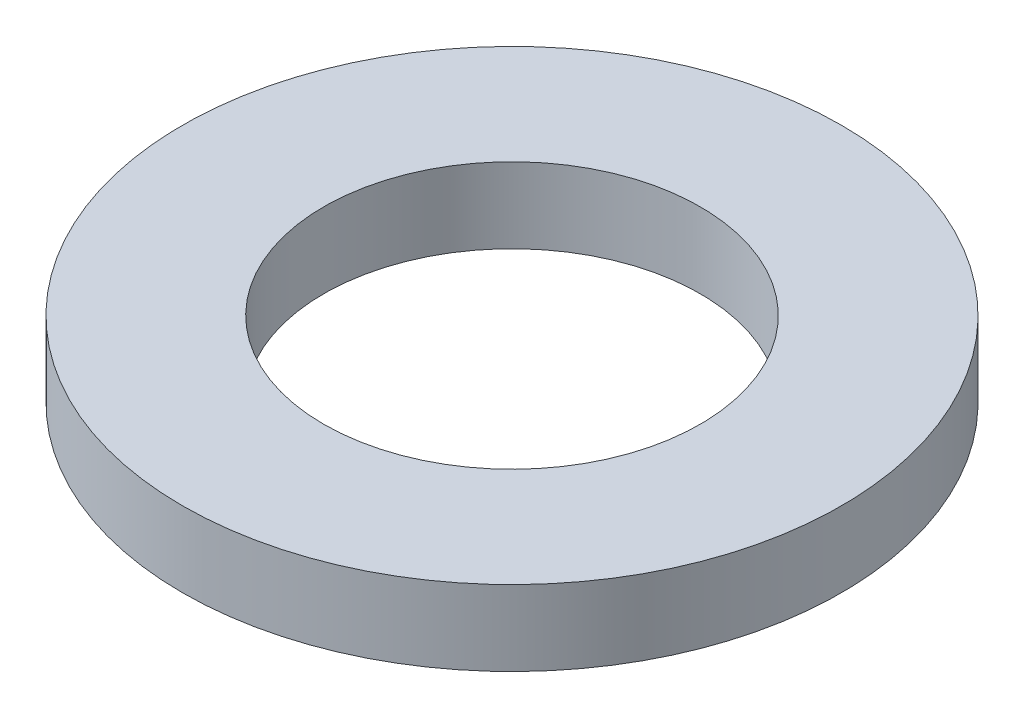
SolidWorks part; units mm, degrees
ref_plane "Front Plane" through (0, 0, 0) normal (0, 0, 1) x (1, 0, 0)
ref_plane "Top Plane" through (0, 0, 0) normal (0, 1, 0) x (1, 0, 0)
ref_plane "Right Plane" through (0, 0, 0) normal (1, 0, 0) x (0, 0, -1)
sketch "Sketch1" plane through (0, 0, 0) normal (0, 1, 0) x (1, 0, 0)
  circle A0 centre (0, 0) radius 17.5
  circle A1 centre (0, 0) radius 10
  dimension "D1" = 20
  dimension "D2" = 35
extrude "Boss-Extrude1" add sketch "Sketch1" along normal blind 4
